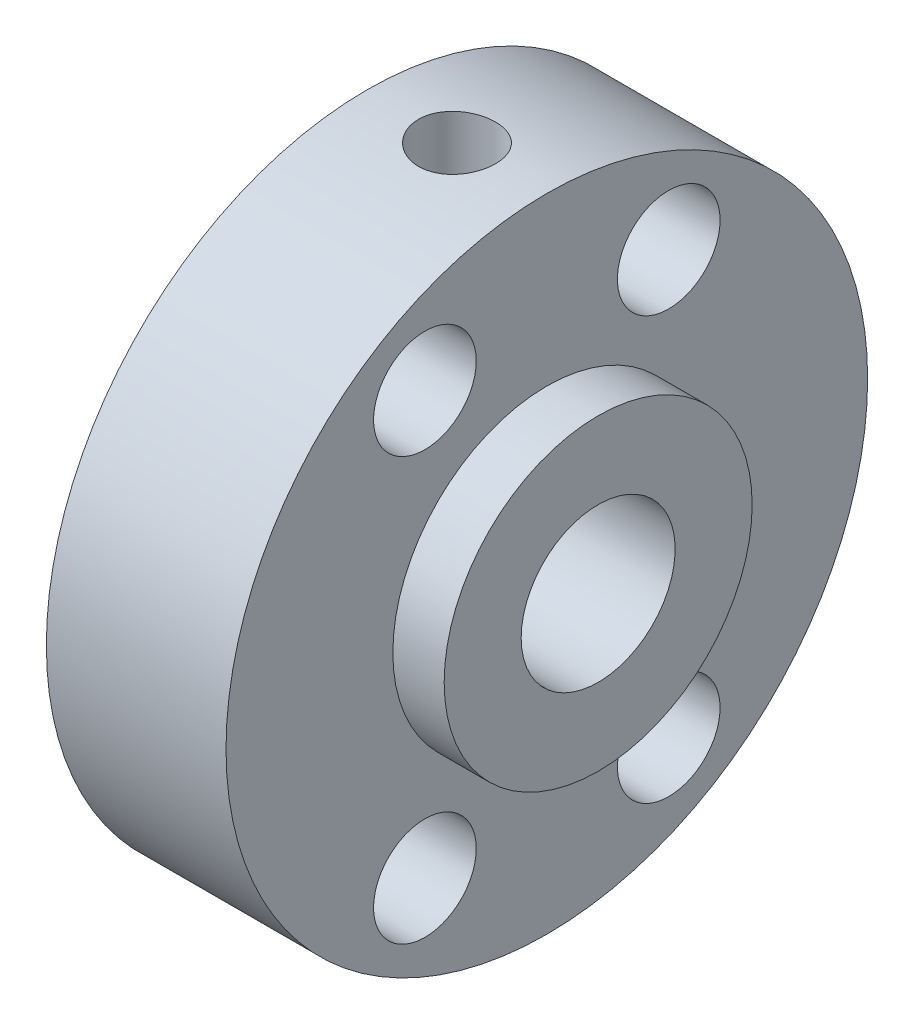
SolidWorks part; units mm, degrees
ref_plane "Plan de face" through (0, 0, 0) normal (0, 0, 1) x (1, 0, 0)
ref_plane "Plan de dessus" through (0, 0, 0) normal (0, 1, 0) x (1, 0, 0)
ref_plane "Plan de droite" through (0, 0, 0) normal (1, 0, 0) x (0, 0, -1)
sketch "Esquisse1" plane through (0, 0, 0) normal (0, 0, 1) x (1, 0, 0)
  line L0 (0, 0) -> (9, 0) construction
  line L1 (0, 3) -> (0, 12.5)
  line L2 (0, 12.5) -> (7, 12.5)
  line L3 (7, 12.5) -> (7, 6)
  line L4 (7, 6) -> (9, 6)
  line L5 (9, 6) -> (9, 3)
  line L6 (9, 3) -> (0, 3)
  dimension "D1" = 6
  dimension "D2" = 9
  dimension "D3" = 7
  dimension "D4" = 25
  dimension "D5" = 12
revolve "Révolution1" add sketch "Esquisse1" angle 360 about L0
sketch "Esquisse2" plane through (7, 0, 0) normal (1, 0, 0) x (0, 0, -1)
  line L0 (-4.75, 8.2272) -> (4.75, -8.2272) construction
  line L1 (4.75, 8.2272) -> (-4.75, -8.2272) construction
  circle A2 centre (-4.75, 8.2272) radius 2
  circle A3 centre (4.75, 8.2272) radius 2
  circle A4 centre (-4.75, -8.2272) radius 2
  circle A5 centre (4.75, -8.2272) radius 2
  point P4 (0, 0)
  dimension "D1" = 60
  dimension "D2" = 9.5
  dimension "D5" = 4
  dimension "D6" = 4
  dimension "D7" = 4
  dimension "D8" = 4
  dimension "D3" = 9.5
  dimension "D4" = 30
extrude "Enlèv. mat.-Extru.1" cut sketch "Esquisse2" against normal through all
sketch "Esquisse3" plane through (0, 0, 0) normal (0, 1, 0) x (1, 0, 0)
  circle A0 centre (3.5, 0) radius 1.5
  dimension "D1" = 3
  dimension "D2" = 3.5
extrude "Enlèv. mat.-Extru.2" cut sketch "Esquisse3" along normal blind 30
